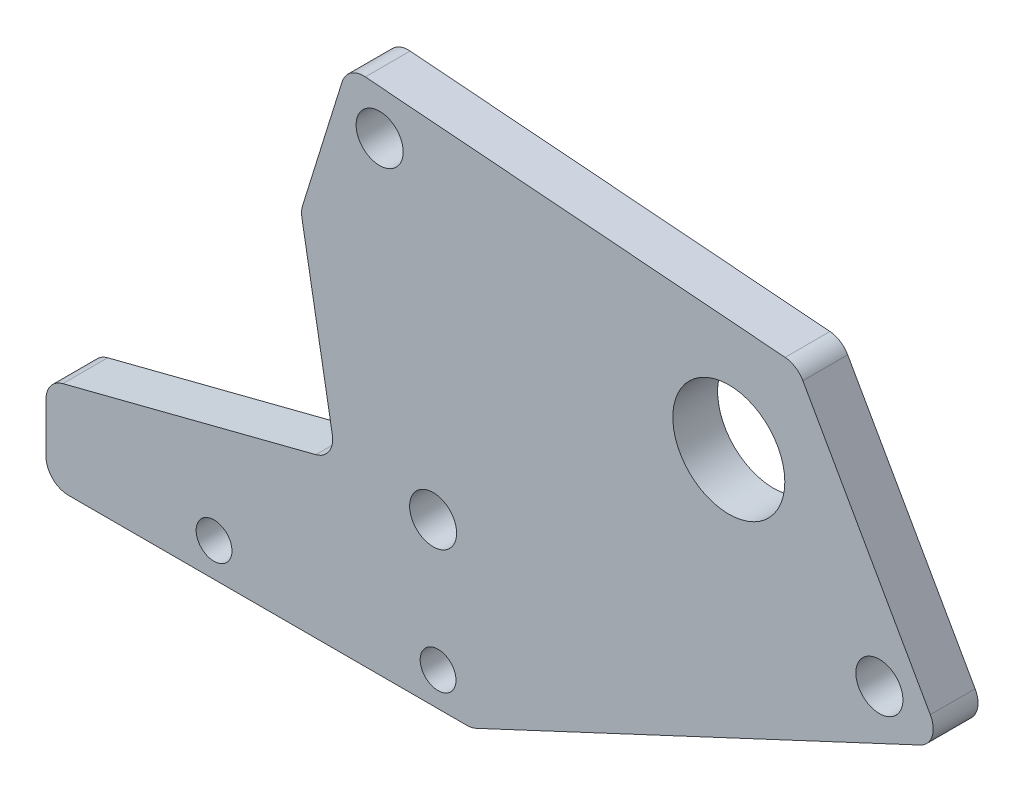
SolidWorks part; units mm, degrees
material "PMMA"
ref_plane "Front Plane" through (0, 0, 0) normal (0, 0, 1) x (1, 0, 0)
ref_plane "Top Plane" through (0, 0, 0) normal (0, 1, 0) x (1, 0, 0)
ref_plane "Right Plane" through (0, 0, 0) normal (1, 0, 0) x (0, 0, -1)
sketch "Sketch1" plane through (0, 0, 0) normal (0, 0, 1) x (1, 0, 0)
  line L0 (-3.4438, 14.4) -> (-8.2191, 41.4822) construction
  line L1 (-3.4438, 14.4) -> (36.3917, 21.4241) construction
  line L2 (-8.2191, 41.4822) -> (31.6164, 48.5063) construction
  line L3 (36.3917, 21.4241) -> (31.6164, 48.5063) construction
  line L4 (-3.4438, 14.4) -> (31.6164, 48.5063) construction
  line L5 (-8.2191, 41.4822) -> (36.3917, 21.4241) construction
  line L6 (14.0863, 31.4531) -> (22.9496, 33.016) construction
  line L7 (0, 0) -> (-38, 0)
  line L9 (-11.0891, 45.7199) -> (29.0377, 42.5686)
  line L10 (29.0377, 42.5686) -> (42, 19.6299)
  line L11 (42, 19.6299) -> (0, 0)
  line L12 (-23, 3) -> (-3, 3) construction
  line L13 (-19.121, 51.4812) -> (-11.2217, 6.6821) construction
  line L14 (-11.2217, 6.6821) -> (53.8598, 18.1578) construction
  line L15 (-15.2442, 32.3739) -> (-12.1185, 14.6474)
  line L18 (-11.0891, 45.7199) -> (-15.2442, 32.3739)
  line L19 (-38, 0) -> (-38, 8)
  line L20 (-38, 8) -> (-12.1185, 14.6474)
  circle A0 centre (-8.2191, 41.4822) radius 2.1
  circle A1 centre (-3.4438, 14.4) radius 2.1
  circle A2 centre (36.3917, 21.4241) radius 2.1
  circle A3 centre (31.6164, 48.5063) radius 2.1 construction
  circle A4 centre (22.9496, 33.016) radius 5
  circle A5 centre (-23, 3) radius 1.6
  circle A6 centre (-3, 3) radius 1.6
  point P1 (14.0863, 31.4531)
  point P28 (-12.9868, 45.8688)
  point P29 (-9.9659, 45.6317)
  dimension "D3" = 4.2
  dimension "D5" = 10
  dimension "D8" = 3.2
  dimension "D10" = 20
  dimension "D11" = 4
  dimension "D12" = 4
  dimension "D13" = 4
  dimension "D14" = 8
  dimension "D15" = 10
  dimension "D16" = 10
  dimension "D1" = 40.45
  dimension "D2" = 27.5
  dimension "D4" = 9
  dimension "D6" = 10
  dimension "D7" = 14.4
  dimension "D9" = 3
  dimension "D17" = 42
  dimension "D18" = 1
  dimension "D19" = 3
  dimension "D20" = 9
  dimension "D21" = 6.25
  dimension "D22" = 8
  dimension "D23" = 15
  dimension "D24" = 4
  dimension "D25" = 18
extrude "Boss-Extrude1" add sketch "Sketch1" along normal blind 4
fillet "Fillet1" radius 2 8 edges at (0, 0, 2) (29.0377, 42.5686, 2) (42, 19.6299, 2) (-11.0891, 45.7199, 2) (-15.2442, 32.3739, 2) (-38, 0, 2) (-38, 8, 2) (-12.1185, 14.6474, 2)
